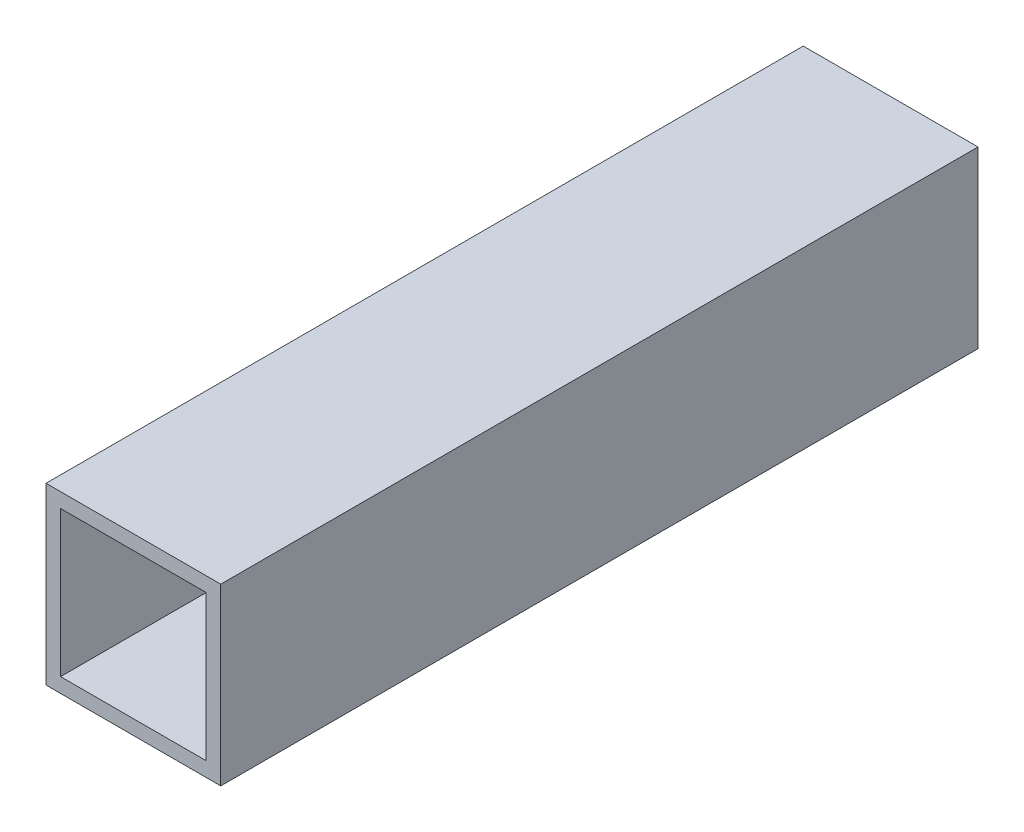
SolidWorks part; units mm, degrees
ref_plane "Alzado" through (0, 0, 0) normal (0, 0, 1) x (1, 0, 0)
ref_plane "Planta" through (0, 0, 0) normal (0, 1, 0) x (1, 0, 0)
ref_plane "Vista lateral" through (0, 0, 0) normal (1, 0, 0) x (0, 0, -1)
sketch "Croquis2" plane through (0, 0, 0) normal (0, 0, 1) x (1, 0, 0)
  line L0 (-7.9375, 7.9375) -> (-7.9375, -7.9375)
  line L1 (9.525, 9.525) -> (-9.525, 9.525)
  line L2 (9.525, 9.525) -> (9.525, -9.525)
  line L3 (9.525, -9.525) -> (-9.525, -9.525)
  line L4 (-9.525, 9.525) -> (-9.525, -9.525)
  line L5 (9.525, 9.525) -> (-9.525, -9.525) construction
  line L6 (9.525, -9.525) -> (-9.525, 9.525) construction
  line L7 (7.9375, -7.9375) -> (-7.9375, -7.9375)
  line L8 (7.9375, 7.9375) -> (7.9375, -7.9375)
  line L9 (7.9375, 7.9375) -> (-7.9375, 7.9375)
  point P0 (0, 0)
  dimension "D1" = 19.05
  dimension "D2" = 19.05
  dimension "D3" = 1.5875
extrude "Saliente-Extruir1" add sketch "Croquis2" along normal mid plane 82.55
